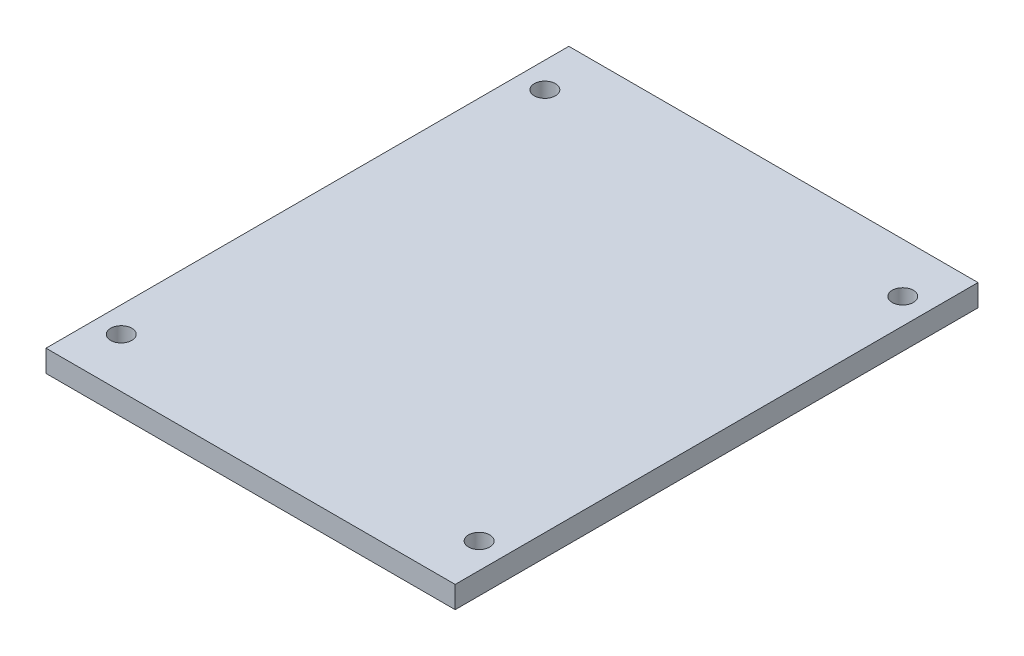
SolidWorks part; units mm, degrees
ref_plane "Front Plane" through (0, 0, 0) normal (0, 0, 1) x (1, 0, 0)
ref_plane "Top Plane" through (0, 0, 0) normal (0, 1, 0) x (1, 0, 0)
ref_plane "Right Plane" through (0, 0, 0) normal (1, 0, 0) x (0, 0, -1)
sketch "Sketch1" plane through (0, 0, 0) normal (0, 1, 0) x (1, 0, 0)
  line L1 (-28.01, -35.79) -> (28.01, -35.79)
  line L2 (-28.01, -35.79) -> (-28.01, 35.79)
  line L3 (-28.01, 35.79) -> (28.01, 35.79)
  line L4 (28.01, -35.79) -> (28.01, 35.79)
  line L5 (-28.01, -35.79) -> (28.01, 35.79) construction
  line L6 (-28.01, 35.79) -> (28.01, -35.79) construction
  line L7 (-24.5, -29) -> (24.5, -29) construction
  line L8 (-24.5, -29) -> (-24.5, 29) construction
  line L9 (-24.5, 29) -> (24.5, 29) construction
  line L10 (24.5, -29) -> (24.5, 29) construction
  line L11 (-24.5, -29) -> (24.5, 29) construction
  line L12 (-24.5, 29) -> (24.5, -29) construction
  circle A0 centre (-24.5, 29) radius 1.45
  circle A1 centre (-24.5, -29) radius 1.45
  circle A2 centre (24.5, -29) radius 1.45
  circle A3 centre (24.5, 29) radius 1.45
  point P0 (0, 0)
  point P6 (0, 0)
  dimension "D3" = 2.9
  dimension "D1" = 56.02
  dimension "D2" = 71.58
  dimension "D4" = 49
  dimension "D5" = 58
extrude "Boss-Extrude1" add sketch "Sketch1" along normal blind 3
